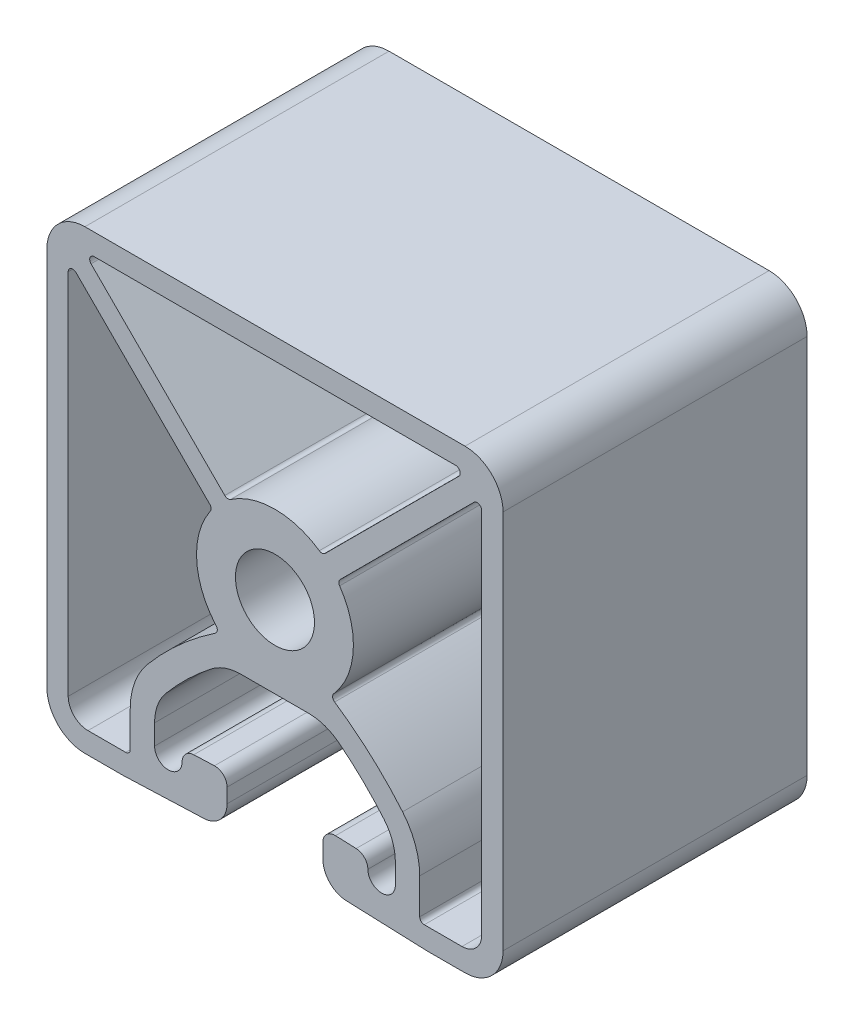
SolidWorks part; units mm, degrees
material "6061 Alloy"
ref_plane "Front" through (0, 0, 0) normal (0, 0, 1) x (1, 0, 0)
ref_plane "Top" through (0, 0, 0) normal (0, 1, 0) x (1, 0, 0)
ref_plane "Right" through (0, 0, 0) normal (1, 0, 0) x (0, 0, -1)
sketch "Sketch1" plane through (0, 0, 0) normal (0, 0, 1) x (1, 0, 0)
  line L0 (2.8281, -6.8072) -> (0, -6.8072)
  line L1 (-2.8281, -6.8072) -> (0, -6.8072)
  line L2 (10.0584, -13.9316) -> (10.0584, -15.6146)
  line L3 (-10.0584, -13.9316) -> (-10.0584, -15.6146)
  line L4 (6.7827, -14.6032) -> (5.0555, -14.5368)
  line L5 (-6.7827, -14.6032) -> (-5.0555, -14.5368)
  line L6 (4.0005, -15.5521) -> (4.0005, -16.7604)
  line L7 (-4.0005, -15.5521) -> (-4.0005, -16.7604)
  line L8 (12.7, -19.05) -> (5.9545, -18.7909)
  line L9 (15.875, -19.05) -> (12.7, -19.05)
  line L10 (-12.7, -19.05) -> (-5.9545, -18.7909)
  line L11 (-15.875, -19.05) -> (-12.7, -19.05)
  line L12 (19.05, 15.875) -> (19.05, -15.875)
  line L13 (-19.05, 15.875) -> (-19.05, -15.875)
  line L14 (0, 19.05) -> (15.875, 19.05)
  line L15 (0, 19.05) -> (-15.875, 19.05)
  line L16 (4.1917, 5.4489) -> (15.3644, 16.6216)
  line L17 (-4.1917, 5.4489) -> (-15.3644, 16.6216)
  line L18 (0, 17.272) -> (15.0949, 17.272)
  line L19 (0, 17.272) -> (-15.0949, 17.272)
  line L20 (-17.272, 15.0949) -> (-17.272, -15.621)
  line L21 (-15.621, -17.272) -> (-12.4714, -17.272)
  line L22 (-5.4489, 4.1917) -> (-16.6216, 15.3644)
  line L23 (-12.0904, -13.9316) -> (-12.0904, -16.891)
  line L24 (17.272, 15.0949) -> (17.272, -15.621)
  line L25 (5.4489, 4.1917) -> (16.6216, 15.3644)
  line L26 (15.621, -17.272) -> (12.4714, -17.272)
  line L27 (12.0904, -13.9316) -> (12.0904, -16.891)
  arc A0 (5.3359, -7.6732) -> (2.8281, -6.8072) centre (2.8281, -10.8712) ccw
  arc A1 (9.1053, -11.3166) -> (5.3359, -7.6732) centre (-10.3378, -27.6606) ccw
  arc A2 (-2.8281, -6.8072) -> (-5.3359, -7.6732) centre (-2.8281, -10.8712) ccw
  arc A3 (10.0584, -13.9316) -> (9.1053, -11.3166) centre (5.9944, -13.9316) ccw
  arc A4 (-5.3359, -7.6732) -> (-9.1053, -11.3166) centre (10.3378, -27.6606) ccw
  arc A5 (-9.1053, -11.3166) -> (-10.0584, -13.9316) centre (-5.9944, -13.9316) ccw
  arc A6 (7.7597, -15.6167) -> (10.0584, -15.6146) centre (8.909, -15.6146) ccw
  arc A7 (7.7597, -15.6167) -> (6.7827, -14.6032) centre (6.7437, -15.6184) ccw
  arc A8 (-10.0584, -15.6146) -> (-7.7597, -15.6167) centre (-8.909, -15.6146) ccw
  arc A9 (-6.7827, -14.6032) -> (-7.7597, -15.6167) centre (-6.7437, -15.6184) ccw
  arc A10 (5.0555, -14.5368) -> (4.0005, -15.5521) centre (5.0165, -15.5521) ccw
  arc A11 (-4.0005, -15.5521) -> (-5.0555, -14.5368) centre (-5.0165, -15.5521) ccw
  arc A12 (4.0005, -16.7604) -> (5.9545, -18.7909) centre (6.0325, -16.7604) ccw
  arc A13 (-5.9545, -18.7909) -> (-4.0005, -16.7604) centre (-6.0325, -16.7604) ccw
  arc A14 (15.875, -19.05) -> (19.05, -15.875) centre (15.875, -15.875) ccw
  arc A15 (-19.05, -15.875) -> (-15.875, -19.05) centre (-15.875, -15.875) ccw
  arc A16 (19.05, 15.875) -> (15.875, 19.05) centre (15.875, 15.875) ccw
  arc A17 (-15.875, 19.05) -> (-19.05, 15.875) centre (-15.875, 15.875) ccw
  arc A18 (0, 3.302) -> (0, -3.302) centre (0, 0) ccw
  arc A19 (0, -3.302) -> (0, 3.302) centre (0, 0) ccw
  arc A20 (3.7067, 5.4041) -> (0, 6.5532) centre (0, 0) ccw
  arc A21 (3.7067, 5.4041) -> (4.1917, 5.4489) centre (3.9223, 5.7183) ccw
  arc A22 (0, 6.5532) -> (-3.7067, 5.4041) centre (0, 0) ccw
  arc A23 (-4.1917, 5.4489) -> (-3.7067, 5.4041) centre (-3.9223, 5.7183) ccw
  arc A24 (15.3644, 16.6216) -> (15.0949, 17.272) centre (15.0949, 16.891) ccw
  arc A25 (-15.0949, 17.272) -> (-15.3644, 16.6216) centre (-15.0949, 16.891) ccw
  arc A26 (-17.272, -15.621) -> (-15.621, -17.272) centre (-15.621, -15.621) ccw
  arc A27 (-16.6216, 15.3644) -> (-17.272, 15.0949) centre (-16.891, 15.0949) ccw
  arc A28 (-12.4714, -17.272) -> (-12.0904, -16.891) centre (-12.4714, -16.891) ccw
  arc A29 (-5.4041, 3.7067) -> (-5.4489, 4.1917) centre (-5.7183, 3.9223) ccw
  arc A30 (-5.4041, 3.7067) -> (-4.9116, -4.3383) centre (0, 0) ccw
  arc A31 (-10.6607, -10.0091) -> (-12.0904, -13.9316) centre (-5.9944, -13.9316) ccw
  arc A32 (-4.9843, -4.9065) -> (-4.9116, -4.3383) centre (-5.1971, -4.5905) ccw
  arc A33 (-4.9843, -4.9065) -> (-10.6607, -10.0091) centre (10.3378, -27.6606) ccw
  arc A34 (17.272, 15.0949) -> (16.6216, 15.3644) centre (16.891, 15.0949) ccw
  arc A35 (15.621, -17.272) -> (17.272, -15.621) centre (15.621, -15.621) ccw
  arc A36 (5.4489, 4.1917) -> (5.4041, 3.7067) centre (5.7183, 3.9223) ccw
  arc A37 (12.0904, -16.891) -> (12.4714, -17.272) centre (12.4714, -16.891) ccw
  arc A38 (4.9116, -4.3383) -> (5.4041, 3.7067) centre (0, 0) ccw
  arc A39 (4.9116, -4.3383) -> (4.9843, -4.9065) centre (5.1971, -4.5905) ccw
  arc A40 (12.0904, -13.9316) -> (10.6607, -10.0091) centre (5.9944, -13.9316) ccw
  arc A41 (10.6607, -10.0091) -> (4.9843, -4.9065) centre (-10.3378, -27.6606) ccw
extrude "Extrude1" add sketch "Sketch1" along normal blind 25.4
